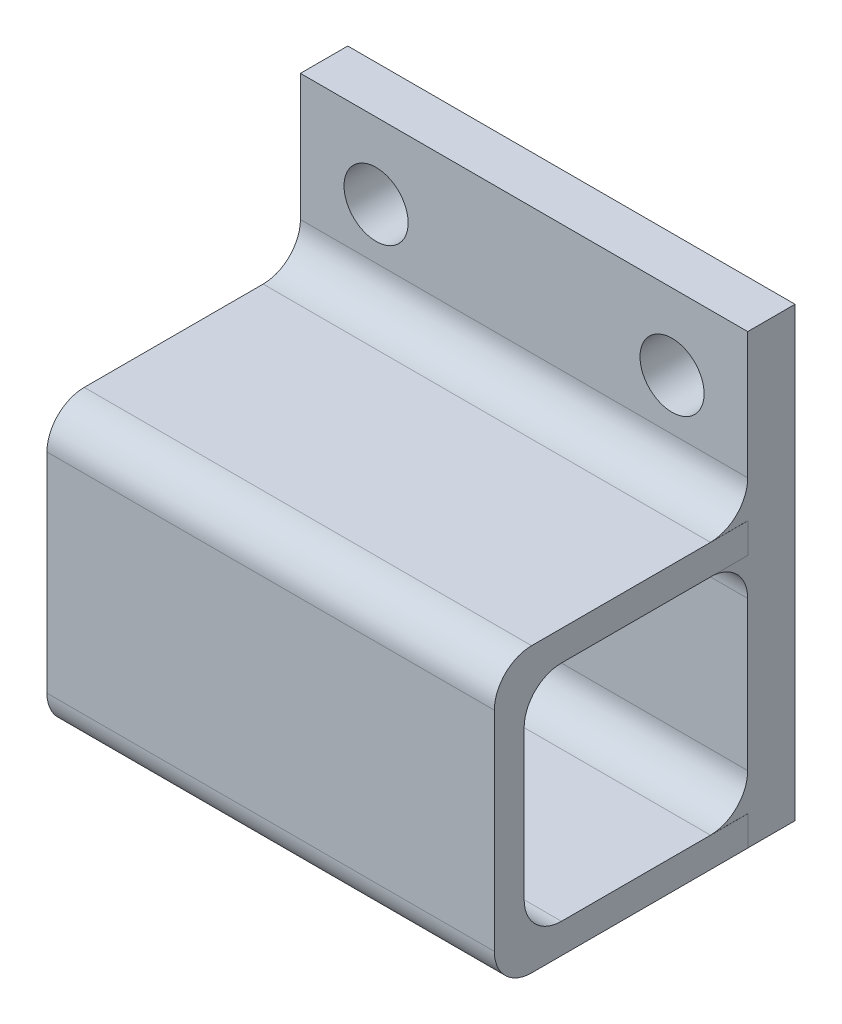
SolidWorks part; units mm, degrees
ref_plane "Front Plane" through (0, 0, 0) normal (0, 0, 1) x (1, 0, 0)
ref_plane "Top Plane" through (0, 0, 0) normal (0, 1, 0) x (1, 0, 0)
ref_plane "Right Plane" through (0, 0, 0) normal (1, 0, 0) x (0, 0, -1)
sketch "Sketch1" plane through (0, 0, 0) normal (0, 0, 1) x (1, 0, 0)
  line L1 (15, -15) -> (-15, -15)
  line L2 (15, -15) -> (15, 15)
  line L3 (15, 15) -> (-15, 15)
  line L4 (-15, -15) -> (-15, 15)
  line L5 (15, -15) -> (-15, 15) construction
  line L6 (15, 15) -> (-15, -15) construction
  circle A0 centre (-9.9249, 9.9249) radius 2.15
  circle A1 centre (9.9249, 9.9249) radius 2.15
  point P0 (0, 0)
  dimension "D3" = 4.3
  dimension "D4" = 4.3
  dimension "D1" = 30
  dimension "D2" = 30
extrude "Boss-Extrude1" add sketch "Sketch1" along normal blind 3.175
sketch "Sketch2" plane through (0, 0, 3.175) normal (0, 0, 1) x (1, 0, 0)
  line L0 (-15, 15) -> (-15, -15) construction
  line L1 (15.0057, -15) -> (-15, -15)
  line L2 (15.0057, -15) -> (15.0057, 4.009)
  line L3 (15.0057, 4.009) -> (-15, 4.009)
  line L4 (-15, -15) -> (-15, 4.009)
  line L5 (15.0057, -15) -> (-15, 4.009) construction
  line L6 (15.0057, 4.009) -> (-15, -15) construction
  line L7 (-15, -15) -> (15, -15) construction
  line L9 (11.8307, -11.825) -> (-11.825, -11.825)
  line L10 (11.8307, -11.825) -> (11.8307, 0.834)
  line L11 (11.8307, 0.834) -> (-11.825, 0.834)
  line L12 (-11.825, -11.825) -> (-11.825, 0.834)
  line L13 (11.8307, -11.825) -> (-11.825, 0.834) construction
  line L14 (11.8307, 0.834) -> (-11.825, -11.825) construction
  point P0 (0.0028, -5.4955)
  point P7 (0.0028, -15)
  point P12 (0.0028, -5.4955)
  dimension "D1" = 3.175
  dimension "D2" = 3.175
  dimension "D3" = 19.009
extrude "Boss-Extrude2" add sketch "Sketch2" along normal blind 15
sketch "Sketch3" plane through (0, 0, 18.175) normal (0, 0, 1) x (1, 0, 0)
  line L1 (-15, 4.009) -> (15.0057, 4.009)
  line L2 (-15, 4.009) -> (-15, -15)
  line L3 (-15, -15) -> (15.0057, -15)
  line L4 (15.0057, 4.009) -> (15.0057, -15)
extrude "Boss-Extrude3" add sketch "Sketch3" along normal blind 2
sketch "Sketch4" plane through (-15, 0, 0) normal (-1, 0, 0) x (0, 0, 1)
  line L0 (20.175, -15) -> (0, -15) construction
  line L1 (3.175, 2) -> (18.175, 2)
  line L2 (3.175, 2) -> (3.175, -13)
  line L3 (3.175, -13) -> (18.175, -13)
  line L4 (18.175, 2) -> (18.175, -13)
  line L6 (0, 15) -> (0, -15) construction
  dimension "D1" = 15
  dimension "D2" = 15
  dimension "D3" = 2
  dimension "D4" = 3.175
extrude "Cut-Extrude1" cut sketch "Sketch4" against normal through all
fillet "Fillet1" radius 2.5 7 edges at (0, 4.009, 3.175) (0.0028, -13, 18.175) (0, 2, 3.175) (0.0028, 2, 18.175) (0, -13, 3.175) (0.0028, -15, 20.175) (0.0028, 4.009, 20.175)
